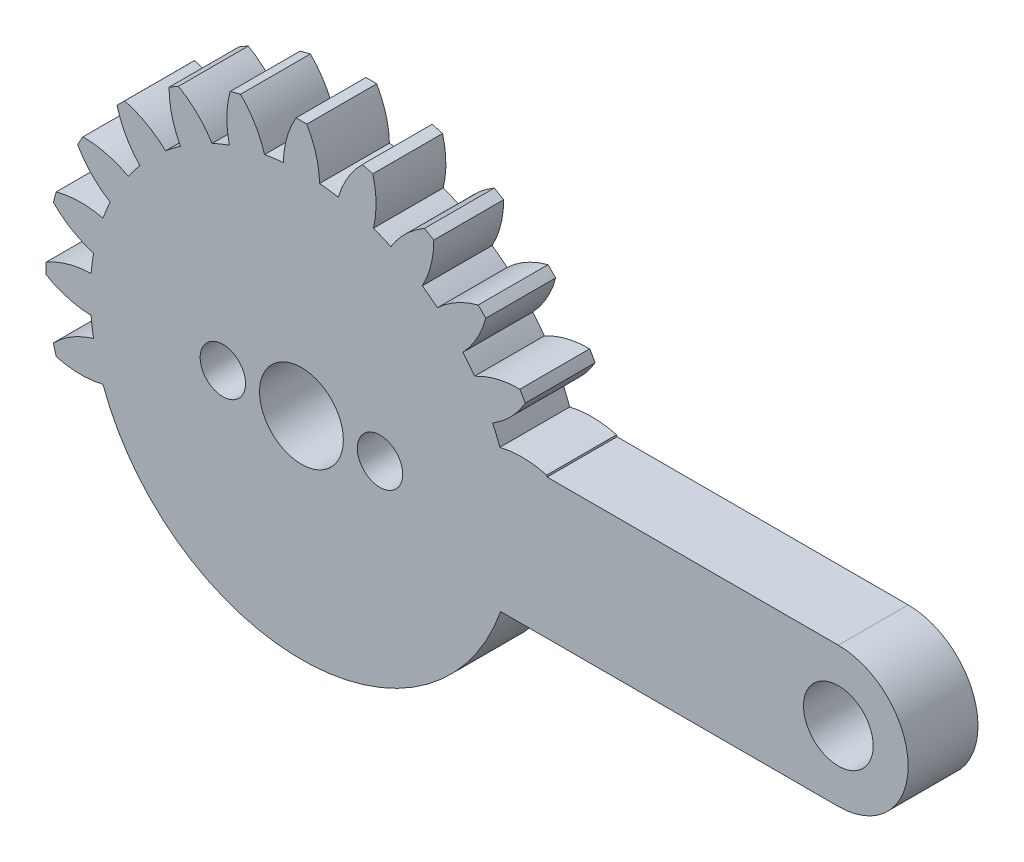
SolidWorks part; units mm, degrees
ref_plane "Front Plane" through (0, 0, 0) normal (0, 0, 1) x (1, 0, 0)
ref_plane "Top Plane" through (0, 0, 0) normal (0, 1, 0) x (1, 0, 0)
ref_plane "Right Plane" through (0, 0, 0) normal (1, 0, 0) x (0, 0, -1)
sketch "Sketch2" plane through (0, 0, 0) normal (0, 0, 1) x (1, 0, 0)
  line L0 (0, 0) -> (0, 14.63) construction
  line L1 (0, 0) -> (34.75, 0) construction
  line L2 (11.4091, 4) -> (30.75, 4)
  line L3 (30.75, -4) -> (11.4091, -4)
  circle A0 centre (0, 0) radius 14.63
  circle A1 centre (0, 0) radius 12.09
  circle A2 centre (0, 0) radius 1.75
  arc A3 (-0.31, 14.6267) -> (-1.04, 12.0452) centre (4.3584, 11.9126) ccw
  arc A4 (0.31, 14.6267) -> (1.04, 12.0452) centre (-4.3584, 11.9126) cw
  arc A5 (3.4862, 14.2086) -> (2.113, 11.9039) centre (7.2931, 10.3787) ccw
  arc A6 (4.0851, 14.0481) -> (4.1221, 11.3656) centre (-1.1267, 12.6347) cw
  arc A7 (7.0449, 12.8221) -> (5.1219, 10.9514) centre (9.7308, 8.1374) ccw
  arc A8 (7.5818, 12.5121) -> (6.9233, 9.9114) centre (2.1819, 12.4958) cw
  arc A9 (10.1234, 10.5619) -> (7.7818, 9.2526) centre (11.5053, 5.3417) ccw
  arc A10 (10.5619, 10.1234) -> (9.2526, 7.7818) centre (5.3417, 11.5053) cw
  arc A11 (12.5121, 7.5818) -> (9.9114, 6.9233) centre (12.4958, 2.1819) ccw
  arc A12 (12.8221, 7.0449) -> (10.9514, 5.1219) centre (8.1374, 9.7308) cw
  arc A13 (14.0481, 4.0851) -> (11.3656, 4.1221) centre (12.6347, -1.1267) ccw
  arc A14 (14.2086, 3.4862) -> (11.9039, 2.113) centre (10.3787, 7.2931) cw
  arc A15 (14.6267, 0.31) -> (12.0452, 1.04) centre (11.9126, -4.3584) ccw
  arc A16 (14.6267, -0.31) -> (12.0452, -1.04) centre (11.9126, 4.3584) cw
  arc A17 (14.2086, -3.4862) -> (11.9039, -2.113) centre (10.3787, -7.2931) ccw
  arc A18 (14.0481, -4.0851) -> (11.3656, -4.1221) centre (12.6347, 1.1267) cw
  arc A19 (12.8221, -7.0449) -> (10.9514, -5.1219) centre (8.1374, -9.7308) ccw
  arc A20 (12.5121, -7.5818) -> (9.9114, -6.9233) centre (12.4958, -2.1819) cw
  arc A21 (10.5619, -10.1234) -> (9.2526, -7.7818) centre (5.3417, -11.5053) ccw
  arc A22 (10.1234, -10.5619) -> (7.7818, -9.2526) centre (11.5053, -5.3417) cw
  arc A23 (7.5818, -12.5121) -> (6.9233, -9.9114) centre (2.1819, -12.4958) ccw
  arc A24 (7.0449, -12.8221) -> (5.1219, -10.9514) centre (9.7308, -8.1374) cw
  arc A25 (4.0851, -14.0481) -> (4.1221, -11.3656) centre (-1.1267, -12.6347) ccw
  arc A26 (3.4862, -14.2086) -> (2.113, -11.9039) centre (7.2931, -10.3787) cw
  arc A27 (0.31, -14.6267) -> (1.04, -12.0452) centre (-4.3584, -11.9126) ccw
  arc A28 (-0.31, -14.6267) -> (-1.04, -12.0452) centre (4.3584, -11.9126) cw
  arc A29 (-3.4862, -14.2086) -> (-2.113, -11.9039) centre (-7.2931, -10.3787) ccw
  arc A30 (-4.0851, -14.0481) -> (-4.1221, -11.3656) centre (1.1267, -12.6347) cw
  arc A31 (-7.0449, -12.8221) -> (-5.1219, -10.9514) centre (-9.7308, -8.1374) ccw
  arc A32 (-7.5818, -12.5121) -> (-6.9233, -9.9114) centre (-2.1819, -12.4958) cw
  arc A33 (-10.1234, -10.5619) -> (-7.7818, -9.2526) centre (-11.5053, -5.3417) ccw
  arc A34 (-10.5619, -10.1234) -> (-9.2526, -7.7818) centre (-5.3417, -11.5053) cw
  arc A35 (-12.5121, -7.5818) -> (-9.9114, -6.9233) centre (-12.4958, -2.1819) ccw
  arc A36 (-12.8221, -7.0449) -> (-10.9514, -5.1219) centre (-8.1374, -9.7308) cw
  arc A37 (-14.0481, -4.0851) -> (-11.3656, -4.1221) centre (-12.6347, 1.1267) ccw
  arc A38 (-14.2086, -3.4862) -> (-11.9039, -2.113) centre (-10.3787, -7.2931) cw
  arc A39 (-14.6267, -0.31) -> (-12.0452, -1.04) centre (-11.9126, 4.3584) ccw
  arc A40 (-14.6267, 0.31) -> (-12.0452, 1.04) centre (-11.9126, -4.3584) cw
  arc A41 (-14.2086, 3.4862) -> (-11.9039, 2.113) centre (-10.3787, 7.2931) ccw
  arc A42 (-14.0481, 4.0851) -> (-11.3656, 4.1221) centre (-12.6347, -1.1267) cw
  arc A43 (-12.8221, 7.0449) -> (-10.9514, 5.1219) centre (-8.1374, 9.7308) ccw
  arc A44 (-12.5121, 7.5818) -> (-9.9114, 6.9233) centre (-12.4958, 2.1819) cw
  arc A45 (-10.5619, 10.1234) -> (-9.2526, 7.7818) centre (-5.3417, 11.5053) ccw
  arc A46 (-10.1234, 10.5619) -> (-7.7818, 9.2526) centre (-11.5053, 5.3417) cw
  arc A47 (-7.5818, 12.5121) -> (-6.9233, 9.9114) centre (-2.1819, 12.4958) ccw
  arc A48 (-7.0449, 12.8221) -> (-5.1219, 10.9514) centre (-9.7308, 8.1374) cw
  arc A49 (-4.0851, 14.0481) -> (-4.1221, 11.3656) centre (1.1267, 12.6347) ccw
  arc A50 (-3.4862, 14.2086) -> (-2.113, 11.9039) centre (-7.2931, 10.3787) cw
  arc A51 (30.75, 4) -> (30.75, -4) centre (30.75, 0) cw
  circle A52 centre (30.75, 0) radius 1.995
  point P154 (0, 0)
  dimension "D1" = 3.5
  dimension "D2" = 24.18
  dimension "D3" = 29.26
  dimension "D4" = 0.62
  dimension "D6" = 5.4
  dimension "D8" = 30.75
  dimension "D9" = 4
  dimension "D10" = 3.99
  dimension "D5" = 2.08
  dimension "D7" = 24
extrude "Boss-Extrude1" add sketch "Sketch2" along normal blind 4 contours A1 | A0 A13 A1 L2 | A14 A0 L2 A1 | A15 A0 A14 A1 | A16 A0 A15 A1 | A17 A0 A16 A1 | A0 A17 A1 L3 | A51 L2 A0 L3 A52 | A12 A0 A11 A1 | A38 A0 A37 A1 | A40 A0 A39 A1 | A42 A0 A41 A1 | A44 A0 A43 A1 | A46 A0 A45 A1 | A48 A0 A47 A1 | A50 A0 A49 A1 | A4 A0 A3 A1 | A6 A0 A5 A1 | A8 A0 A7 A1 | A10 A0 A9 A1
sketch "Sketch4" plane through (0, 0, 4) normal (0, 0, 1) x (1, 0, 0)
  circle A0 centre (4.5, 0) radius 1.3
  circle A1 centre (-4.5, 0) radius 1.3
  circle A2 centre (0, 0) radius 2.4
  dimension "D1" = 4.5
  dimension "D3" = 2.6
  dimension "D4" = 4.8
  dimension "D2" = 9
extrude "Cut-Extrude1" cut sketch "Sketch4" against normal through all
